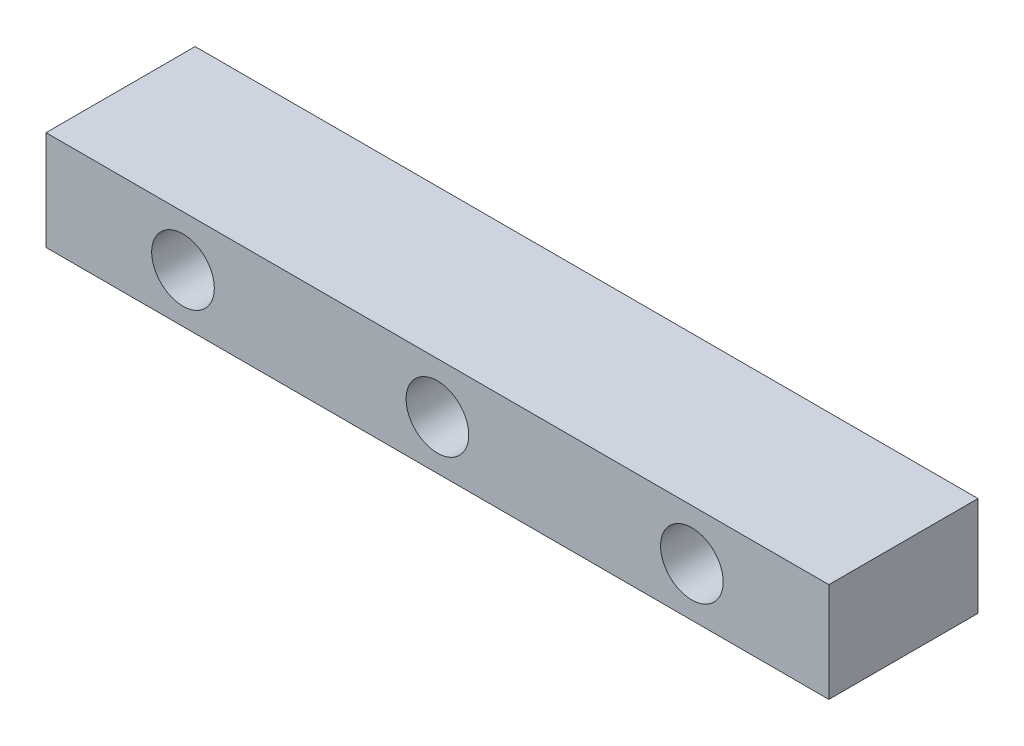
SolidWorks part; units mm, degrees
ref_plane "Front Plane" through (0, 0, 0) normal (0, 0, 1) x (1, 0, 0)
ref_plane "Top Plane" through (0, 0, 0) normal (0, 1, 0) x (1, 0, 0)
ref_plane "Right Plane" through (0, 0, 0) normal (1, 0, 0) x (0, 0, -1)
sketch "Sketch1" plane through (0, 0, 0) normal (0, 1, 0) x (1, 0, 0)
  line L1 (0, 0) -> (400, 0)
  line L2 (0, 0) -> (0, 76.2)
  line L3 (0, 76.2) -> (400, 76.2)
  line L4 (400, 0) -> (400, 76.2)
  dimension "D1" = 400
  dimension "D2" = 76.2
extrude "Boss-Extrude1" add sketch "Sketch1" along normal blind 50.8
sketch "Sketch2" plane through (0, 0, 0) normal (0, 0, 1) x (1, 0, 0)
  line L0 (70, 25) -> (200, 25)
  line L1 (0, 0) -> (70, 0)
  line L2 (0, 0) -> (0, 25)
  line L3 (0, 25) -> (70, 25)
  line L4 (70, 0) -> (70, 25)
  line L5 (200, 25) -> (330, 25)
  circle A0 centre (70, 25) radius 16
  circle A1 centre (200, 25) radius 16
  circle A2 centre (330, 25) radius 16
  dimension "D1" = 70
  dimension "D2" = 25
  dimension "D3" = 130
  dimension "D4" = 130
extrude "Cut-Extrude1" cut sketch "Sketch2" against normal blind 76.2 contours A0 | A1 | A2
